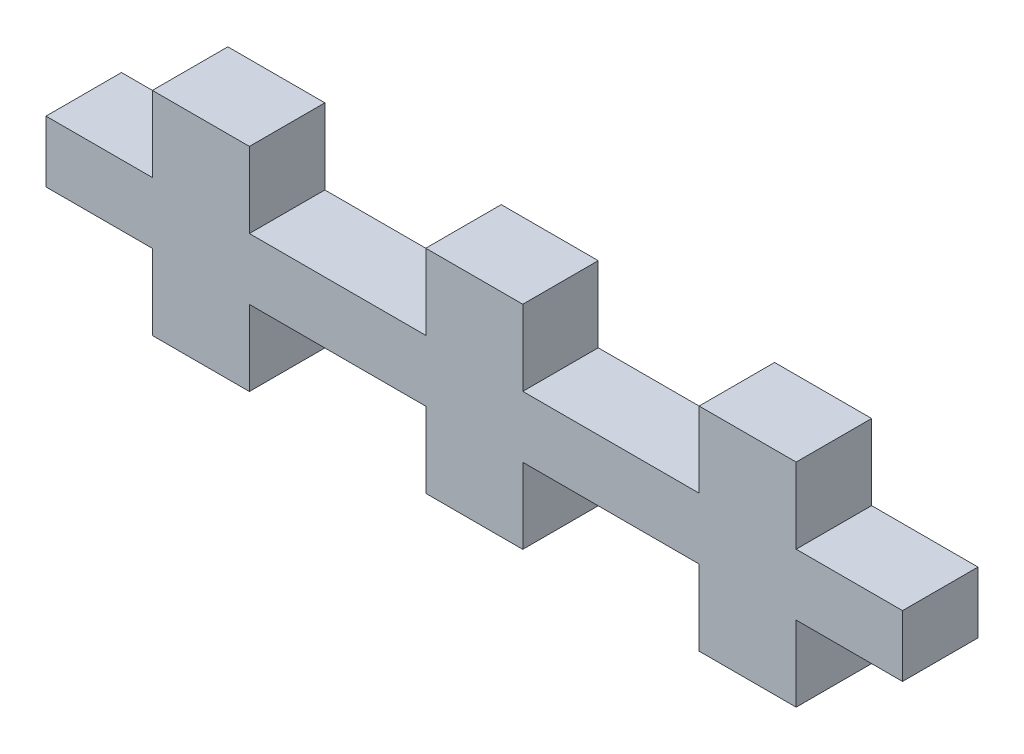
SolidWorks part; units mm, degrees
ref_plane "Front Plane" through (0, 0, 0) normal (0, 0, 1) x (1, 0, 0)
ref_plane "Top Plane" through (0, 0, 0) normal (0, 1, 0) x (1, 0, 0)
ref_plane "Right Plane" through (0, 0, 0) normal (1, 0, 0) x (0, 0, -1)
sketch "Sketch1" plane through (0, 0, 0) normal (0, 0, 1) x (1, 0, 0)
  line L2 (-21.15, 1.25) -> (21.15, 1.25) construction
  line L3 (-21.15, 0) -> (21.15, 0)
  line L4 (-21.15, 0) -> (-21.15, 2.5)
  line L5 (-21.15, 2.5) -> (21.15, 2.5)
  line L6 (21.15, 0) -> (21.15, 2.5)
  line L9 (-2, 5.675) -> (2, 2.5) construction
  line L16 (-2, 2.5) -> (2, 5.675) construction
  line L17 (2, 2.5) -> (2, 5.675)
  line L18 (-2, 0) -> (-2, -3.175)
  line L19 (-13.5, 0) -> (-13.5, -3.175)
  line L20 (-13.5, -3.175) -> (-9.5, -3.175)
  line L21 (-9.5, 0) -> (-9.5, -3.175)
  line L22 (13.5, 0) -> (13.5, -3.175)
  line L23 (13.5, -3.175) -> (9.5, -3.175)
  line L24 (9.5, 0) -> (9.5, -3.175)
  line L25 (-2, -3.175) -> (2, -3.175)
  line L26 (2, 0) -> (2, -3.175)
  line L27 (-2, 0) -> (2, -3.175) construction
  line L28 (-2, -3.175) -> (2, 0) construction
  line L29 (-2, 0) -> (2, 0)
  line L31 (-2, 5.675) -> (2, 5.675)
  line L32 (9.5, 2.5) -> (9.5, 5.675)
  line L43 (13.5, 5.675) -> (9.5, 5.675)
  line L44 (13.5, 2.5) -> (13.5, 5.675)
  line L48 (-9.5, 2.5) -> (-9.5, 5.675)
  line L49 (-13.5, 5.675) -> (-9.5, 5.675)
  line L50 (-13.5, 2.5) -> (-13.5, 5.675)
  line L51 (-2, 2.5) -> (-2, 5.675)
  point P4 (0, 0)
  point P19 (0, 4.0875)
  point P28 (0, -1.5875)
  point P33 (0, 0)
  dimension "D7" = 4
  dimension "D8" = 3.175
  dimension "D9" = 7.5
  dimension "D10" = 7.5
  dimension "D2" = 42.3
  dimension "D3" = 2.5
extrude "Boss-Extrude1" add sketch "Sketch1" along normal blind 3.175 contours L21 L3 L19 L20 | L50 L5 L48 L49 | L51 L5 L17 L31 | L26 L3 L18 L25 | L5 L44 L43 L32 | L3 L24 L23 L22 | L3 L6 L5 L4
sketch "Sketch2" plane through (0, 2.5, 0) normal (0, 1, 0) x (1, 0, 0)
  line L0 (-21.15, -3.175) -> (-13.5, -3.175) construction
  line L1 (-21.15, 0) -> (-17.975, 0)
  line L2 (-21.15, 0) -> (-21.15, -3.175)
  line L3 (-21.15, -3.175) -> (-17.975, -3.175)
  line L4 (-17.975, 0) -> (-17.975, -3.175)
  line L5 (13.5, -3.175) -> (21.15, -3.175) construction
  line L6 (21.15, 0) -> (17.975, 0)
  line L7 (21.15, 0) -> (21.15, -3.175)
  line L8 (21.15, -3.175) -> (17.975, -3.175)
  line L9 (17.975, 0) -> (17.975, -3.175)
  line L10 (-21.15, -3.175) -> (-17.975, 0)
  line L11 (21.15, -3.175) -> (17.975, 0)
  line M4 (-13.5, 0) -> (-21.15, 0)
  line M5 (-21.15, 0) -> (-21.15, -3.175)
  line M6 (-21.15, -3.175) -> (-13.5, -3.175)
  dimension "D1" = 3.175
  dimension "D2" = 3.175
extrude "Cut-Extrude2" cut sketch "Sketch2" against normal blind 23.175 contours L10 M5 M4 | L10 L4 M6 | L8 L11 L9 | L11 L7 L6
sketch "Sketch3" plane through (0, 0, 3.175) normal (0, 0, 1) x (1, 0, 0)
  line L56 (-13.5406, 2.5406) -> (-18.0156, 2.5406)
  line L57 (-18.0156, 2.5406) -> (-18.0156, -0.0406)
  line L58 (-18.0156, -0.0406) -> (-13.5406, -0.0406)
  line L59 (-13.5406, -0.0406) -> (-13.5406, -3.2156)
  line L60 (-13.5406, -3.2156) -> (-9.4594, -3.2156)
  line L61 (-9.4594, -3.2156) -> (-9.4594, -0.0406)
  line L62 (-9.4594, -0.0406) -> (-2.0406, -0.0406)
  line L63 (-2.0406, -0.0406) -> (-2.0406, -3.2156)
  line L64 (-2.0406, -3.2156) -> (2.0406, -3.2156)
  line L65 (2.0406, -3.2156) -> (2.0406, -0.0406)
  line L66 (2.0406, -0.0406) -> (9.4594, -0.0406)
  line L67 (9.4594, -0.0406) -> (9.4594, -3.2156)
  line L68 (9.4594, -3.2156) -> (13.5406, -3.2156)
  line L69 (13.5406, -3.2156) -> (13.5406, -0.0406)
  line L70 (13.5406, -0.0406) -> (18.0156, -0.0406)
  line L71 (18.0156, -0.0406) -> (18.0156, 2.5406)
  line L72 (18.0156, 2.5406) -> (13.5406, 2.5406)
  line L73 (13.5406, 2.5406) -> (13.5406, 5.7156)
  line L74 (13.5406, 5.7156) -> (9.4594, 5.7156)
  line L75 (9.4594, 5.7156) -> (9.4594, 2.5406)
  line L76 (9.4594, 2.5406) -> (2.0406, 2.5406)
  line L77 (2.0406, 2.5406) -> (2.0406, 5.7156)
  line L78 (2.0406, 5.7156) -> (-2.0406, 5.7156)
  line L79 (-2.0406, 5.7156) -> (-2.0406, 2.5406)
  line L80 (-2.0406, 2.5406) -> (-9.4594, 2.5406)
  line L81 (-9.4594, 2.5406) -> (-9.4594, 5.7156)
  line L82 (-9.4594, 5.7156) -> (-13.5406, 5.7156)
  line L83 (-13.5406, 5.7156) -> (-13.5406, 2.5406)
  line L84 (-13.5406, 2.5406) -> (-18.0156, 2.5406)
  line L85 (-18.0156, 2.5406) -> (-18.0156, -0.0406)
  line L86 (-18.0156, -0.0406) -> (-13.5406, -0.0406)
  line L87 (-13.5406, -0.0406) -> (-13.5406, -3.2156)
  line L88 (-13.5406, -3.2156) -> (-9.4594, -3.2156)
  line L89 (-9.4594, -3.2156) -> (-9.4594, -0.0406)
  line L90 (-9.4594, -0.0406) -> (-2.0406, -0.0406)
  line L91 (-2.0406, -0.0406) -> (-2.0406, -3.2156)
  line L92 (-2.0406, -3.2156) -> (2.0406, -3.2156)
  line L93 (2.0406, -3.2156) -> (2.0406, -0.0406)
  line L94 (2.0406, -0.0406) -> (9.4594, -0.0406)
  line L95 (9.4594, -0.0406) -> (9.4594, -3.2156)
  line L96 (9.4594, -3.2156) -> (13.5406, -3.2156)
  line L97 (13.5406, -3.2156) -> (13.5406, -0.0406)
  line L98 (13.5406, -0.0406) -> (18.0156, -0.0406)
  line L99 (18.0156, -0.0406) -> (18.0156, 2.5406)
  line L100 (18.0156, 2.5406) -> (13.5406, 2.5406)
  line L101 (13.5406, 2.5406) -> (13.5406, 5.7156)
  line L102 (13.5406, 5.7156) -> (9.4594, 5.7156)
  line L103 (9.4594, 5.7156) -> (9.4594, 2.5406)
  line L104 (9.4594, 2.5406) -> (2.0406, 2.5406)
  line L105 (2.0406, 2.5406) -> (2.0406, 5.7156)
  line L106 (2.0406, 5.7156) -> (-2.0406, 5.7156)
  line L107 (-2.0406, 5.7156) -> (-2.0406, 2.5406)
  line L108 (-2.0406, 2.5406) -> (-9.4594, 2.5406)
  line L109 (-9.4594, 2.5406) -> (-9.4594, 5.7156)
  line L110 (-9.4594, 5.7156) -> (-13.5406, 5.7156)
  line L111 (-13.5406, 5.7156) -> (-13.5406, 2.5406)
  dimension "D1" = 0.0406
extrude "Boss-Extrude2" add sketch "Sketch3" against normal blind 3.175
equation "\"stepper width\"=4.23"
equation "\"stepper hole disctance\" = 3.1"
equation "\"stepper hole diameter\"=0.34"
equation "\"stepper shaft hole\"=2.4"
equation "\"tooth width\"=0.4"
equation "\"tooth thickness\"=0.3175"
equation "\"tooth to side\"=0.75"
equation "\"motor chamber height\" = 6"
equation "\"D2@Sketch1\"=\"stepper width\""
equation "\"D3@Sketch1\"=(3 - \"stepper width\"/2) - (\"tooth thickness\"*2)"
equation "\"D1@Sketch2\"=\"tooth thickness\""
equation "\"D2@Sketch2\"=\"tooth thickness\""
